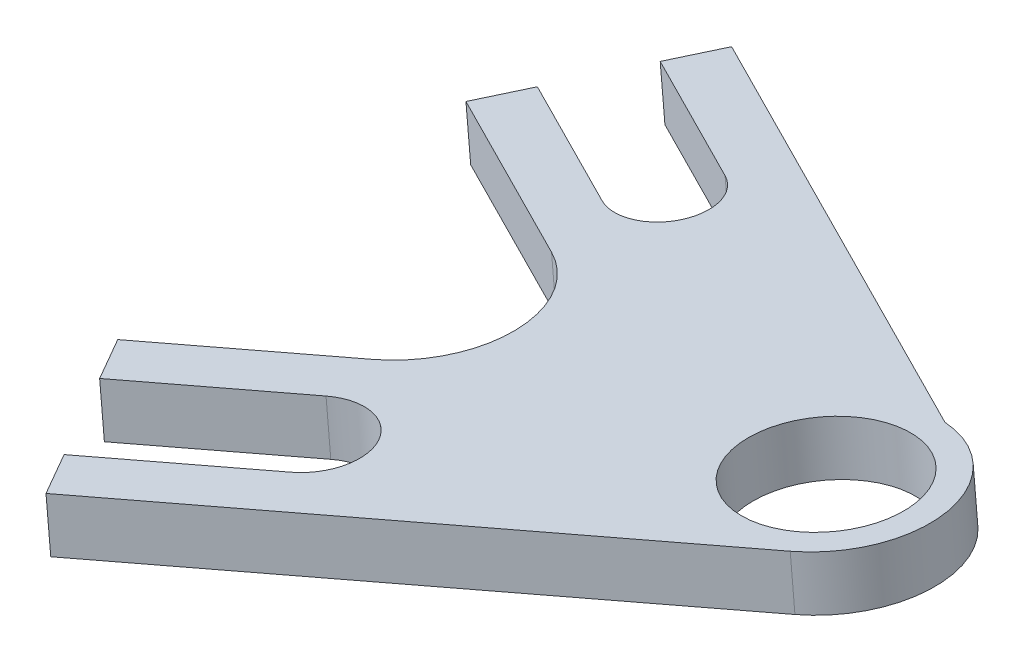
SolidWorks part; units mm, degrees
ref_plane "Front" through (0, 0, 0) normal (0, 0, 1) x (1, 0, 0)
ref_plane "Top" through (0, 0, 0) normal (0, 1, 0) x (1, 0, 0)
ref_plane "Right" through (0, 0, 0) normal (1, 0, 0) x (0, 0, -1)
sketch "Sketch1" plane through (-54.1554, 613.8788, 32.9927) normal (-0.09, 0.9959, 0) x (0, 0, 1)
  line L0 (-29.6236, 535.8256) -> (1.896, 593.2881)
  line L2 (173.6932, 326.2554) -> (14.3245, 591.3872) construction
  line L3 (-131.1068, 326.2554) -> (14.3245, 591.3872) construction
  line L4 (173.6932, 326.2554) -> (14.3245, 591.3872) construction
  line L5 (-131.1068, 326.2554) -> (14.3245, 591.3872) construction
  line L7 (-29.6236, 535.8256) -> (-24.0561, 532.7718)
  line L8 (-8.9127, 524.4652) -> (22.6069, 581.9277)
  line L9 (-26.8398, 534.2987) -> (2.3582, 587.5288) construction
  line L10 (-8.9127, 524.4652) -> (-14.4801, 527.5191)
  line L11 (-24.0561, 532.7718) -> (-14.467, 550.2535)
  line L12 (-14.4801, 527.5191) -> (-4.891, 545.0009)
  line L13 (-14.467, 550.2535) -> (-9.679, 547.6272) construction
  line L14 (3.5484, 584.9098) -> (37.3133, 528.7373)
  line L15 (37.3133, 528.7373) -> (42.7558, 532.0087)
  line L16 (37.8171, 552.304) -> (32.4835, 549.098) construction
  line L17 (42.7558, 532.0087) -> (32.4835, 549.098)
  line L18 (53.423, 538.4207) -> (43.1507, 555.51)
  line L19 (58.8654, 541.6921) -> (53.423, 538.4207)
  line L20 (25.1005, 597.8647) -> (58.8654, 541.6921)
  line L21 (-17.4081, 558.0954) -> (3.3028, 546.735) construction
  line L22 (23.8351, 551.1602) -> (45.3872, 564.115) construction
  circle A0 centre (14.3245, 591.3872) radius 9.398
  circle A1 centre (14.3245, 591.3872) radius 12.573
  arc A2 (-14.467, 550.2535) -> (-4.891, 545.0009) centre (-9.679, 547.6272) cw
  arc A3 (32.4835, 549.098) -> (43.1507, 555.51) centre (37.8171, 552.304) cw
  point P8 (-17.0944, 534.1083)
  point P9 (-7.0526, 552.4152)
  point P31 (0, 0)
  point P32 (0, 0)
  point P33 (21.8575, 567.353)
  point P34 (0, 0)
  dimension "D1" = 18.796
  dimension "D2" = 3.175
  dimension "D3" = 8.636
  dimension "D4" = 6.35
  dimension "D5" = 25.4
  dimension "D6" = 44.45
  dimension "D7" = 59.756
extrude "Boss-Extrude1" add sketch "Sketch1" along normal mid plane 6.35 contours L11 A2 L12 L10 L8 L14 A1 L0 L7 | A1 L14 L8 | L17 A3 L18 L19 L20 A1 L8 L14 L15 | A1 A0
fillet "Fillet1" radius 12.7 1 edges at (510.4513, 664.9175, 47.3614)
